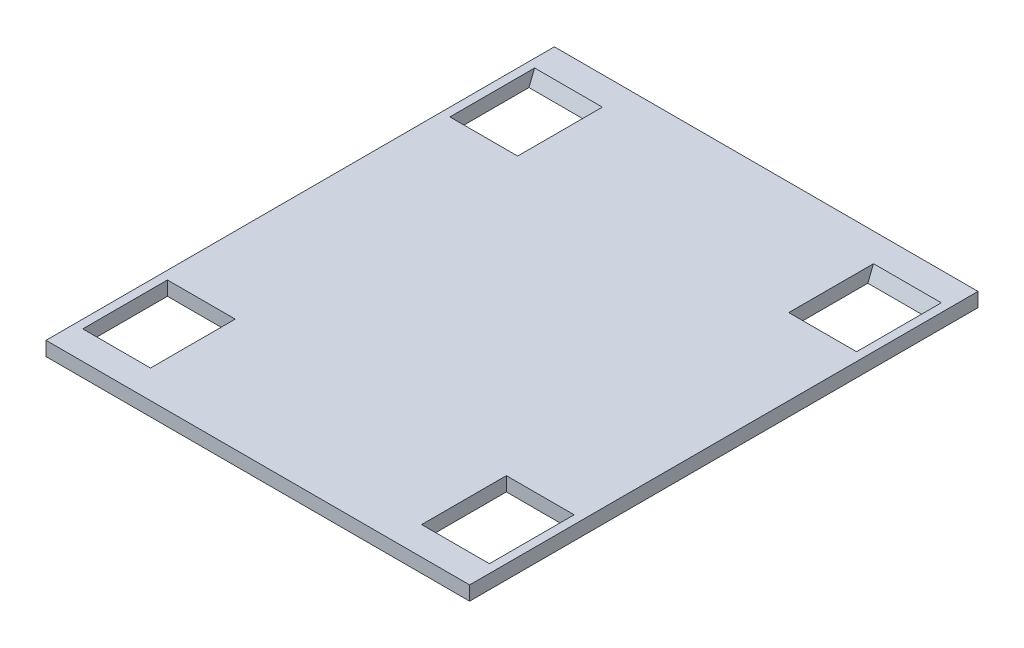
SolidWorks part; units mm, degrees
ref_plane "Front Plane" through (0, 0, 0) normal (0, 0, 1) x (1, 0, 0)
ref_plane "Top Plane" through (0, 0, 0) normal (0, 1, 0) x (1, 0, 0)
ref_plane "Right Plane" through (0, 0, 0) normal (1, 0, 0) x (0, 0, -1)
sketch "Sketch1" plane through (0, 0, 0) normal (0, 1, 0) x (1, 0, 0)
  line L1 (-95.25, 114.3) -> (95.25, 114.3)
  line L2 (-95.25, 114.3) -> (-95.25, -114.3)
  line L3 (-95.25, -114.3) -> (95.25, -114.3)
  line L4 (95.25, 114.3) -> (95.25, -114.3)
  line L5 (-95.25, 114.3) -> (95.25, -114.3) construction
  line L6 (-95.25, -114.3) -> (95.25, 114.3) construction
  point P0 (0, 0)
  dimension "D1" = 190.5
  dimension "D2" = 228.6
extrude "Boss-Extrude1" add sketch "Sketch1" along normal blind 6.35
sketch "Sketch2" plane through (0, 6.35, 0) normal (0, 1, 0) x (1, 0, 0)
  line L0 (-95.25, 114.3) -> (-95.25, -114.3) construction
  line L1 (-91.44, 101.6) -> (-60.96, 101.6)
  line L2 (-91.44, 101.6) -> (-91.44, 63.5)
  line L3 (-91.44, 63.5) -> (-60.96, 63.5)
  line L4 (-60.96, 101.6) -> (-60.96, 63.5)
  line L10 (95.25, 114.3) -> (-95.25, 114.3) construction
  line L11 (0, 114.3) -> (0, -62.491) construction
  line L12 (-95.25, 0) -> (95.25, 0) construction
  line L13 (95.25, -114.3) -> (95.25, 114.3) construction
  line L14 (-91.44, -63.5) -> (-60.96, -63.5)
  line L15 (-60.96, -101.6) -> (-60.96, -63.5)
  line L16 (-91.44, -101.6) -> (-60.96, -101.6)
  line L17 (-91.44, -101.6) -> (-91.44, -63.5)
  line L18 (91.44, -101.6) -> (91.44, -63.5)
  line L19 (91.44, -101.6) -> (60.96, -101.6)
  line L20 (60.96, -101.6) -> (60.96, -63.5)
  line L21 (91.44, -63.5) -> (60.96, -63.5)
  line L22 (91.44, 63.5) -> (60.96, 63.5)
  line L23 (60.96, 101.6) -> (60.96, 63.5)
  line L24 (91.44, 101.6) -> (60.96, 101.6)
  line L25 (91.44, 101.6) -> (91.44, 63.5)
  dimension "D1" = 38.1
  dimension "D2" = 30.48
  dimension "D3" = 3.81
  dimension "D4" = 50.8
extrude "Cut-Extrude1" cut sketch "Sketch2" against normal up to next
sketch "Sketch3" plane through (91.44, 0, 0) normal (-1, 0, 0) x (0, 0, 1)
  line L3 (-101.6, 6.35) -> (-101.6, 0)
  line L4 (-101.6, 6.35) -> (-99.06, 0)
  line L5 (-101.6, 0) -> (-63.5, 0) construction
  line L6 (-99.06, 0) -> (-101.6, 0)
  dimension "D1" = 2.54
extrude "Boss-Extrude2" add sketch "Sketch3" along normal up to next (30.48 mm away)
mirror "Mirror1" about plane through (0, 0, 0) normal (0, 0, 1) of "Boss-Extrude2"
mirror "Mirror2" about plane through (0, 0, 0) normal (1, 0, 0) of "Mirror1", "Boss-Extrude2"
